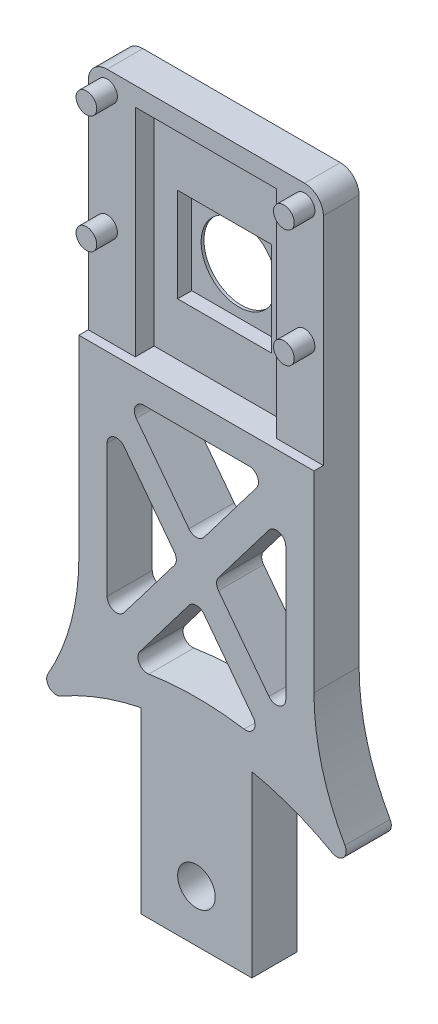
SolidWorks part; units mm, degrees
ref_plane "Ebene vorne" through (0, 0, 0) normal (0, 0, 1) x (1, 0, 0)
ref_plane "Ebene oben" through (0, 0, 0) normal (0, 1, 0) x (1, 0, 0)
ref_plane "Ebene rechts" through (0, 0, 0) normal (1, 0, 0) x (0, 0, -1)
sketch "Skizze1" plane through (0, 0, 0) normal (0, 0, 1) x (1, 0, 0)
  line L1 (-12.5, 75) -> (12.5, 75)
  line L2 (-12.5, 75) -> (-12.5, 0)
  line L3 (-12.5, 0) -> (12.5, 0)
  line L4 (12.5, 75) -> (12.5, 0)
  line L5 (-12.5, 75) -> (12.5, 0) construction
  line L6 (-12.5, 0) -> (12.5, 75) construction
  point P0 (0, 37.5)
  dimension "D1" = 75
  dimension "D2" = 25
extrude "Aufsatz-Linear austragen1" add sketch "Skizze1" along normal blind 4.8
sketch "Skizze2" plane through (0, 0, 4.8) normal (0, 0, 1) x (1, 0, 0)
  line L0 (12.5, 75) -> (-12.5, 75) construction
  line L1 (10.5, 60.5) -> (-10.5, 60.5)
  line L2 (10.5, 60.5) -> (10.5, 73)
  line L3 (10.5, 73) -> (-10.5, 73)
  line L4 (-10.5, 60.5) -> (-10.5, 73)
  line L5 (10.5, 60.5) -> (-10.5, 73) construction
  line L6 (10.5, 73) -> (-10.5, 60.5) construction
  circle A0 centre (-10.5, 73) radius 1.1
  circle A1 centre (-10.5, 60.5) radius 1.1
  circle A2 centre (10.5, 60.5) radius 1.1
  circle A3 centre (10.5, 73) radius 1.1
  point P0 (0, 66.75)
  point P5 (0, 60.5)
  dimension "D4" = 2.2
  dimension "D1" = 21
  dimension "D2" = 12.5
  dimension "D3" = 8.25
extrude "Schnitt-Linear austragen1" cut sketch "Skizze2" against normal blind 5 contours L4 A0 L3 | L2 A3 L3 | L3 A3 L2 | L4 A1 L1 | L1 A1 L4 | L1 A2 L2 | L2 A2 L1 | L3 A0 L4
sketch "Skizze3" plane through (0, 0, 4.8) normal (0, 0, 1) x (1, 0, 0)
  line L0 (12.5, 75) -> (-12.5, 75) construction
  line L1 (-12.5, 75) -> (12.5, 75)
  line L2 (-12.5, 75) -> (-12.5, 50)
  line L3 (-12.5, 50) -> (12.5, 50)
  line L4 (12.5, 75) -> (12.5, 50)
  line L5 (12.5, 0) -> (12.5, 75) construction
  line L6 (-12.5, 75) -> (-12.5, 0) construction
  dimension "D1" = 25
extrude "Schnitt-Linear austragen2" cut sketch "Skizze3" against normal blind 1
sketch "Skizze4" plane through (0, 0, 3.8) normal (0, 0, 1) x (1, 0, 0)
  line L0 (-12.5, 50) -> (12.5, 50) construction
  line L1 (-7.5, 50) -> (7.5, 50)
  line L2 (-7.5, 50) -> (-7.5, 73)
  line L3 (-7.5, 73) -> (7.5, 73)
  line L4 (7.5, 50) -> (7.5, 73)
  line L6 (-12.5, 50) -> (12.5, 50) construction
  line L7 (-12.5, 50) -> (12.5, 50)
  line L8 (7.5, 50) -> (-7.5, 73) construction
  line L9 (7.5, 73) -> (-7.5, 50) construction
  point P8 (0, 61.5)
  point P10 (0, 50)
  point P11 (7.5, 50)
  line M6 (-12.5, 50) -> (12.5, 50)
  dimension "D1" = 23
  dimension "D2" = 15
extrude "Schnitt-Linear austragen3" cut sketch "Skizze4" against normal blind 2 contours L4 L3 L2 M6
sketch "Skizze5" plane through (0, 0, 1.8) normal (0, 0, 1) x (1, 0, 0)
  line L0 (-7.5, 50) -> (7.5, 50) construction
  line L1 (-7.5, 73) -> (7.5, 73) construction
  circle A0 centre (0, 60.6) radius 4
  point P7 (0, 73)
  dimension "D1" = 8
  dimension "D2" = 10.6
extrude "Schnitt-Linear austragen4" cut sketch "Skizze5" against normal through all
sketch "Skizze6" plane through (0, 0, 1.8) normal (0, 0, 1) x (1, 0, 0)
  line L1 (5, 55.6) -> (-5, 55.6)
  line L2 (5, 55.6) -> (5, 65.6)
  line L3 (5, 65.6) -> (-5, 65.6)
  line L4 (-5, 55.6) -> (-5, 65.6)
  line L5 (5, 55.6) -> (-5, 65.6) construction
  line L6 (5, 65.6) -> (-5, 55.6) construction
  circle A0 centre (0, 60.6) radius 4 construction
  circle A1 centre (0, 60.6) radius 4
  dimension "D1" = 10
  dimension "D2" = 10
extrude "Schnitt-Linear austragen5" cut sketch "Skizze6" against normal blind 1.5
sketch "Skizze7" plane through (0, 0, 0) normal (0, 0, 1) x (1, 0, 0)
  line L1 (10.5, 60.5) -> (-10.5, 60.5)
  line L2 (10.5, 60.5) -> (10.5, 73)
  line L3 (10.5, 73) -> (-10.5, 73)
  line L4 (-10.5, 60.5) -> (-10.5, 73)
  line L5 (10.5, 60.5) -> (-10.5, 73) construction
  line L6 (10.5, 73) -> (-10.5, 60.5) construction
  circle A0 centre (-10.5, 73) radius 1.1
  circle A1 centre (-10.5, 60.5) radius 1.1
  circle A2 centre (10.5, 60.5) radius 1.1
  circle A3 centre (10.5, 73) radius 1.1
  circle A4 centre (-10.5, 60.5) radius 1.1 construction
  circle A5 centre (-10.5, 60.5) radius 1.1
  circle A6 centre (-10.5, 73) radius 1.1 construction
  circle A7 centre (-10.5, 73) radius 1.1
  point P0 (0, 66.75)
  dimension "D4" = 2.2
  dimension "D1" = 21
  dimension "D2" = 12.5
extrude "Aufsatz-Linear austragen2" add sketch "Skizze7" along normal blind 6 contours L4 A1 L1 | L3 A0 L4 | L1 A2 L2 | L2 A3 L3 | L3 A3 L2 | L2 A2 L1 | L1 A1 L4 | L4 A0 L3
sketch "Skizze8" plane through (0, 0, 4.8) normal (0, 0, 1) x (1, 0, 0)
  line L0 (-12.5, 0) -> (12.5, 0) construction
  circle A0 centre (0, 5.5) radius 2
  dimension "D1" = 4
  dimension "D2" = 5.5
extrude "Schnitt-Linear austragen6" cut sketch "Skizze8" against normal through all and the other way through all
sketch "Skizze9" plane through (0, 0, 4.8) normal (0, 0, 1) x (1, 0, 0)
  line L0 (0, 0) -> (0, 33.7865) construction
  line L1 (-12.5, 0) -> (-5.9, 0)
  line L2 (-12.5, 0) -> (-12.5, 19)
  line L3 (-12.5, 19) -> (-5.9, 19)
  line L4 (-5.9, 0) -> (-5.9, 19)
  line L5 (-12.5, 0) -> (12.5, 0) construction
  line L6 (5.9, 0) -> (5.9, 19)
  line L7 (12.5, 19) -> (5.9, 19)
  line L8 (12.5, 0) -> (12.5, 19)
  line L9 (12.5, 0) -> (5.9, 0)
  dimension "D1" = 5.9
  dimension "D2" = 19
extrude "Schnitt-Linear austragen7" cut sketch "Skizze9" against normal through all
sketch "Skizze10" plane through (0, 0, 4.8) normal (0, 0, 1) x (1, 0, 0)
  line L0 (12.5, 19) -> (12.5, 50) construction
  line L2 (12.5, 29.5679) -> (12.5, 50)
  line L3 (-12.5, 49.6105) -> (-12.5, 29.5679)
  line L4 (0, -9.6896) -> (0, 19.6004) construction
  line L6 (-12.5, 50) -> (-12.5, 19) construction
  arc A0 (20.2316, 11.4902) -> (-20.2316, 11.4902) centre (0, -9.6896) ccw
  arc A1 (-20.2316, 11.4902) -> (-12.5, 29.5679) centre (-37.5, 29.5679) ccw
  arc A2 (20.2316, 11.4902) -> (12.5, 29.5679) centre (37.5, 29.5679) cw
  line M1 (-12.5, 19) -> (-5.9, 19)
  line M5 (5.9, 19) -> (12.5, 19)
  line M6 (12.5, 19) -> (12.5, 50)
  line M8 (-12.5, 50) -> (-12.5, 19)
  dimension "D1" = 29.29
  dimension "D2" = 25
extrude "Aufsatz-Linear austragen3" add sketch "Skizze10" against normal up to surface (4.8 mm away) contours A1 A0 M1 M8 | A0 A2 M6 M5 up to face at (2, 5.5, 0)
fillet "Verrundung1" radius 2 2 edges at (-12.5, 75, 1.9) (12.5, 75, 1.9)
fillet "Verrundung2" radius 1 2 edges at (20.2316, 11.4902, 2.4) (-20.2316, 11.4902, 2.4)
sketch "Skizze12" plane through (0, 0, 4.8) normal (0, 0, 1) x (1, 0, 0)
  line L0 (-12.5, 50) -> (-12.5, 29.5679) construction
  line L1 (9.5, 47) -> (-9.5, 47)
  line L2 (9.5, 47) -> (9.5, 22)
  line L3 (9.5, 22) -> (7.616, 22)
  line L4 (-9.5, 47) -> (-9.5, 22)
  line L5 (9.5, 47) -> (-9.5, 22) construction
  line L6 (9.5, 22) -> (-9.5, 47) construction
  line L7 (-7.5, 50) -> (7.5, 50) construction
  line L8 (-9.5, 24.479) -> (-1.884, 34.5)
  line L9 (9.5, 44.521) -> (1.884, 34.5)
  line L10 (7.616, 22) -> (0, 32.021)
  line L11 (-7.616, 47) -> (0, 36.979)
  line L12 (0, 32.021) -> (-7.616, 22)
  line L13 (0, 36.979) -> (7.616, 47)
  line L14 (-1.884, 34.5) -> (-9.5, 44.521)
  line L15 (1.884, 34.5) -> (9.5, 24.479)
  line L16 (-7.616, 22) -> (-9.5, 22)
  arc A0 (-5.9, 19) -> (-14.4334, 15.7973) centre (0, -9.6896) ccw construction
  arc A1 (-5.9, 19) -> (-14.4334, 15.7973) centre (0, -9.6896) ccw
  arc A2 (7.616, 22) -> (-7.616, 22) centre (0, -9.6896) ccw
  point P0 (0, 34.5)
  dimension "D1" = 3
  dimension "D2" = 3
  dimension "D3" = 3
  dimension "D4" = 3
  dimension "D5" = 1.5
extrude "Schnitt-Linear austragen8" cut sketch "Skizze12" against normal through all contours L8 L14 L4 | L11 L13 L1 | L9 L15 L2 | A2 L10 L12
fillet "Verrundung3" radius 1 12 edges at (7.616, 47, 2.4) (-7.616, 47, 2.4) (0, 36.979, 2.4) (1.884, 34.5, 2.4) (9.5, 44.521, 2.4) (9.5, 24.479, 2.4) (-1.884, 34.5, 2.4) (-9.5, 24.479, 2.4) (-9.5, 44.521, 2.4) (0, 32.021, 2.4) (7.616, 22, 2.4) (-7.616, 22, 2.4)
